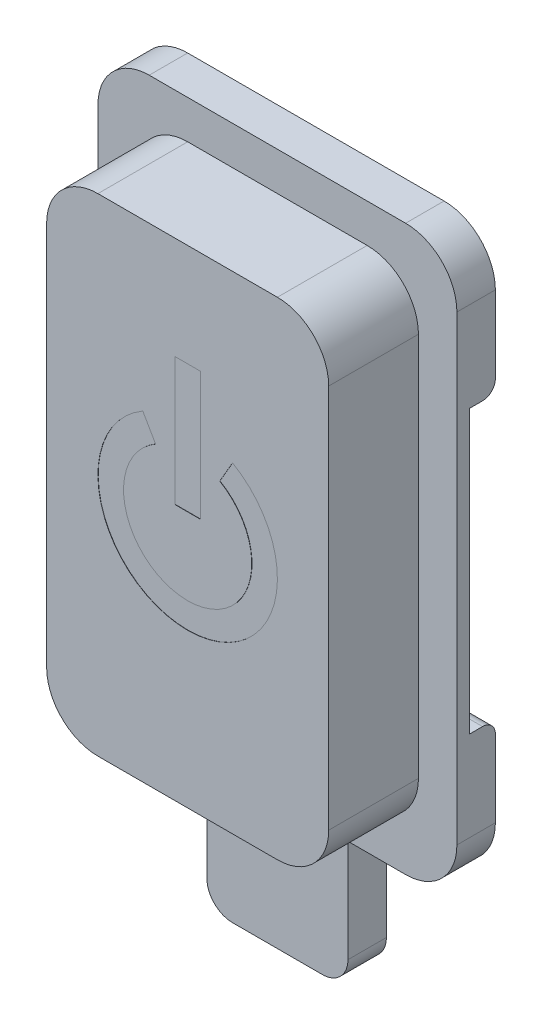
SolidWorks part; units mm, degrees
ref_plane "前视基准面" through (0, 0, 0) normal (0, 0, 1) x (1, 0, 0)
ref_plane "上视基准面" through (0, 0, 0) normal (0, 1, 0) x (1, 0, 0)
ref_plane "右视基准面" through (0, 0, 0) normal (1, 0, 0) x (0, 0, -1)
sketch "草图1" plane through (0, 0, 0) normal (0, 0, 1) x (1, 0, 0)
  line L1 (7, 11) -> (-7, 11)
  line L2 (7, 11) -> (7, -11)
  line L3 (7, -11) -> (-7, -11)
  line L4 (-7, 11) -> (-7, -11)
  line L5 (7, 11) -> (-7, -11) construction
  line L6 (7, -11) -> (-7, 11) construction
  point P0 (0, 0)
  dimension "D1" = 14
  dimension "D2" = 22
extrude "凸台-拉伸1" add sketch "草图1" along normal blind 5
sketch "草图2" plane through (0, 0, 5) normal (0, 0, 1) x (1, 0, 0)
  line L1 (-5.5, 9.5) -> (5.5, 9.5)
  line L2 (-5.5, 9.5) -> (-5.5, -9.5)
  line L3 (-5.5, -9.5) -> (5.5, -9.5)
  line L4 (5.5, 9.5) -> (5.5, -9.5)
  line L5 (-5.5, 9.5) -> (5.5, -9.5) construction
  line L6 (-5.5, -9.5) -> (5.5, 9.5) construction
  point P0 (0, 0)
  dimension "D1" = 11
  dimension "D2" = 19
extrude "切除-拉伸1" cut sketch "草图2" against normal blind 3.5 flip side to cut
sketch "草图3" plane through (0, 0, 0) normal (0, 0, -1) x (-1, 0, 0)
  line L1 (4, 8) -> (-4, 8)
  line L2 (4, 8) -> (4, -8)
  line L3 (4, -8) -> (-4, -8)
  line L4 (-4, 8) -> (-4, -8)
  line L5 (4, 8) -> (-4, -8) construction
  line L6 (4, -8) -> (-4, 8) construction
  point P0 (0, 0)
  dimension "D1" = 8
  dimension "D2" = 16
extrude "切除-拉伸2" cut sketch "草图3" against normal blind 3
sketch "草图4" plane through (0, 0, 0) normal (0, 0, -1) x (-1, 0, 0)
  line L0 (7, -11) -> (-7, -11) construction
  line L1 (-2.75, -11) -> (2.75, -11)
  line L2 (-2.75, -11) -> (-2.75, -16)
  line L3 (-2.75, -16) -> (2.75, -16)
  line L4 (2.75, -11) -> (2.75, -16)
  line L5 (0, 0) -> (0, -6.0022) construction
  dimension "D1" = 5.5
  dimension "D2" = 5
extrude "凸台-拉伸2" add sketch "草图4" against normal up to surface (1.5 mm away) up to face at (0, 0, 1.5)
fillet "圆角1" radius 2 8 edges at (5.5, 9.5, 3.25) (-5.5, 9.5, 3.25) (7, -11, 0.75) (5.5, -9.5, 3.25) (-7, -11, 0.75) (-5.5, -9.5, 3.25) (-7, 11, 0.75) (7, 11, 0.75)
fillet "圆角2" radius 1 6 edges at (4, -8, 1.5) (-4, -8, 1.5) (4, 8, 1.5) (-4, 8, 1.5) (-2.75, -16, 0.75) (2.75, -16, 0.75)
sketch "草图5" plane through (0, 0, 0) normal (0, 0, -1) x (-1, 0, 0)
  line L0 (0, 0) -> (0, -6.226) construction
  line L1 (-2, -11) -> (-0.5, -11)
  line L2 (-2, -11) -> (-2, -12)
  line L3 (-2, -12) -> (-0.5, -12)
  line L4 (2, -11) -> (2, -12)
  line L5 (-0.5, -9.5) -> (0.5, -9.5)
  line L6 (-0.5, -9.5) -> (-0.5, -11)
  line L7 (-0.5, -13.5) -> (0.5, -13.5)
  line L8 (0.5, -9.5) -> (0.5, -11)
  line L9 (-1.75, -16) -> (1.75, -16) construction
  line L10 (-0.5, -11.5) -> (0.5, -11.5) construction
  line L11 (0.5, -11) -> (2, -11)
  line L12 (-0.5, -12) -> (-0.5, -13.5)
  line L13 (0.5, -12) -> (2, -12)
  line L14 (0.5, -12) -> (0.5, -13.5)
  dimension "D1" = 1
  dimension "D2" = 4
  dimension "D3" = 2.5
extrude "凸台-拉伸3" add sketch "草图5" along normal blind 4
sketch "草图6" plane through (0, 0, 5) normal (0, 0, 1) x (1, 0, 0)
  line L0 (-1.25, 2.1651) -> (-1.75, 3.0311)
  line L1 (1.25, 2.1651) -> (1.75, 3.0311)
  line L2 (0, 0) -> (0, 5.1065) construction
  line L4 (-0.5, 5.5) -> (0.5, 5.5)
  line L5 (-0.5, 5.5) -> (-0.5, 0.5)
  line L6 (-0.5, 0.5) -> (0.5, 0.5)
  line L7 (0.5, 5.5) -> (0.5, 0.5)
  arc A0 (-1.25, 2.1651) -> (1.25, 2.1651) centre (0, 0) ccw
  arc A1 (-1.75, 3.0311) -> (1.75, 3.0311) centre (0, 0) ccw
  dimension "D1" = 5
  dimension "D2" = 7
  dimension "D3" = 60
  dimension "D4" = 1
  dimension "D5" = 5
  dimension "D6" = 0.5
extrude "切除-拉伸3" cut sketch "草图6" against normal blind 0.01
sketch "草图7" plane through (0, 0, 0) normal (0, 0, -1) x (-1, 0, 0)
  line L0 (0, 0) -> (-10.7396, 0) construction
  line L1 (-7, -9) -> (-7, 9) construction
  line L2 (-7, 5.5) -> (-4, 5.5)
  line L3 (-7, 5.5) -> (-7, -5.5)
  line L4 (-7, -5.5) -> (-4, -5.5)
  line L7 (-4, 5.5) -> (-4, -5.5)
  line L8 (-4, 7) -> (-4, -7) construction
  dimension "D1" = 11
extrude "切除-拉伸4" cut sketch "草图7" against normal blind 1
fillet "圆角3" radius 0.5 6 edges at (0, -9.5, -4) (-2, -11.5, -4) (0, -13.5, -4) (2, -11.5, -4) (5.5, -5.5, 0) (5.5, 5.5, 0)
